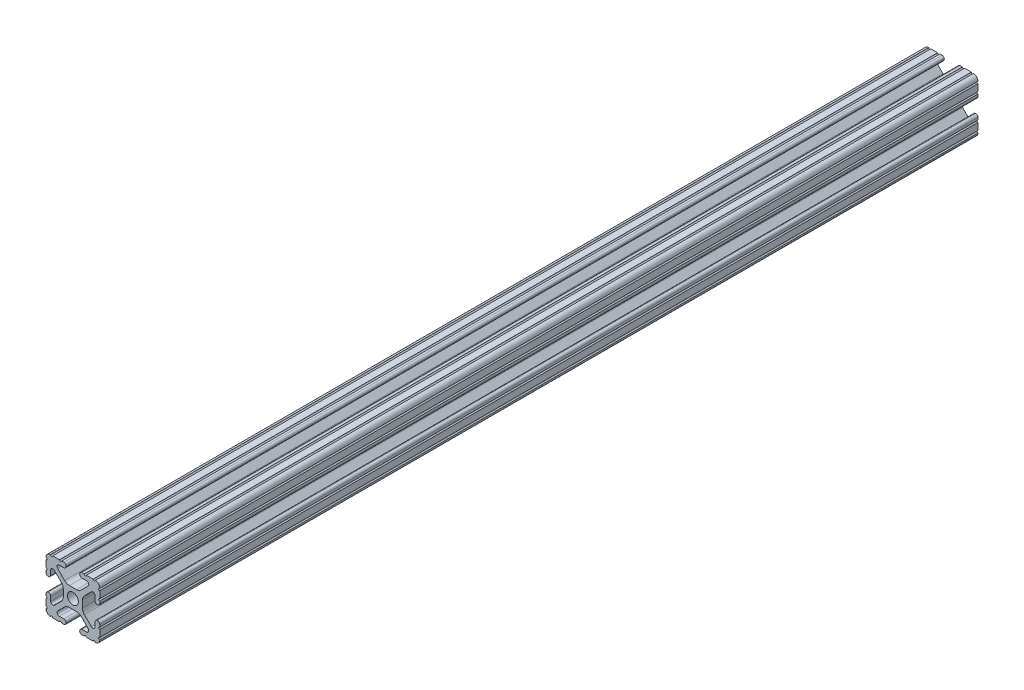
SolidWorks part; units mm, degrees
ref_plane "Front Plane" through (0, 0, 0) normal (0, 0, 1) x (1, 0, 0)
ref_plane "Top Plane" through (0, 0, 0) normal (0, 1, 0) x (1, 0, 0)
ref_plane "Right Plane" through (0, 0, 0) normal (1, 0, 0) x (0, 0, -1)
sketch "Sketch1" plane through (0, 0, 0) normal (0, 0, 1) x (1, 0, 0)
  line L88 (-7.1797, -8.6452) -> (-3.9523, -5.4237)
  line L89 (-1.7093, -4.4958) -> (1.7093, -4.4958)
  line L90 (3.9523, -5.4237) -> (7.1797, -8.6452)
  line L91 (6.4164, -10.4902) -> (4.2875, -10.4902)
  line L92 (3.2385, -11.5392) -> (3.2385, -11.651)
  line L93 (4.2875, -12.7) -> (5.3171, -12.7)
  line L94 (6.3331, -12.7) -> (9.5504, -12.7)
  line L95 (12.7, -9.5504) -> (12.7, -6.3331)
  line L96 (12.7, -5.3171) -> (12.7, -4.2875)
  line L97 (11.651, -3.2385) -> (11.5392, -3.2385)
  line L98 (10.4902, -4.2875) -> (10.4902, -6.4021)
  line L99 (8.7371, -7.1294) -> (5.441, -3.8408)
  line L100 (4.5085, -1.5932) -> (4.5085, 1.5932)
  line L101 (5.441, 3.8408) -> (8.7371, 7.1294)
  line L102 (10.4902, 6.4021) -> (10.4902, 4.2875)
  line L103 (11.5392, 3.2385) -> (11.651, 3.2385)
  line L104 (12.7, 4.2875) -> (12.7, 5.3171)
  line L105 (12.7, 6.3331) -> (12.7, 9.5504)
  line L106 (9.5504, 12.7) -> (6.3331, 12.7)
  line L107 (5.3171, 12.7) -> (4.2875, 12.7)
  line L108 (3.2385, 11.651) -> (3.2385, 11.5392)
  line L109 (4.2875, 10.4902) -> (6.4768, 10.4902)
  line L110 (7.207, 8.7244) -> (3.8983, 5.4232)
  line L111 (1.6558, 4.4958) -> (-1.6558, 4.4958)
  line L112 (-3.8983, 5.4232) -> (-7.207, 8.7244)
  line L113 (-6.4768, 10.4902) -> (-4.2875, 10.4902)
  line L114 (-3.2385, 11.5392) -> (-3.2385, 11.651)
  line L115 (-4.2875, 12.7) -> (-5.3171, 12.7)
  line L116 (-6.3331, 12.7) -> (-9.5504, 12.7)
  line L117 (-12.7, 9.5504) -> (-12.7, 6.3331)
  line L118 (-12.7, 5.3171) -> (-12.7, 4.2875)
  line L119 (-11.651, 3.2385) -> (-11.5392, 3.2385)
  line L120 (-10.4902, 4.2875) -> (-10.4902, 6.4021)
  line L121 (-8.7371, 7.1294) -> (-5.441, 3.8408)
  line L122 (-4.5085, 1.5932) -> (-4.5085, -1.5932)
  line L123 (-5.441, -3.8408) -> (-8.7371, -7.1294)
  line L124 (-10.4902, -6.4021) -> (-10.4902, -4.2875)
  line L125 (-11.5392, -3.2385) -> (-11.651, -3.2385)
  line L126 (-12.7, -4.2875) -> (-12.7, -5.3171)
  line L127 (-12.7, -6.3331) -> (-12.7, -9.5504)
  line L128 (-9.5504, -12.7) -> (-6.3331, -12.7)
  line L129 (-5.3171, -12.7) -> (-4.2875, -12.7)
  line L130 (-3.2385, -11.651) -> (-3.2385, -11.5392)
  line L131 (-4.2875, -10.4902) -> (-6.4164, -10.4902)
  circle A1 centre (0, 0) radius 2.6035
  arc A104 (-7.1797, -8.6452) -> (-6.4164, -10.4902) centre (-6.4164, -9.4098) ccw
  arc A105 (-1.7093, -4.4958) -> (-3.9523, -5.4237) centre (-1.7093, -7.6708) ccw
  arc A106 (3.9523, -5.4237) -> (1.7093, -4.4958) centre (1.7093, -7.6708) ccw
  arc A107 (6.4164, -10.4902) -> (7.1797, -8.6452) centre (6.4164, -9.4098) ccw
  arc A108 (4.2875, -10.4902) -> (3.2385, -11.5392) centre (4.2875, -11.5392) ccw
  arc A109 (3.2385, -11.651) -> (4.2875, -12.7) centre (4.2875, -11.651) ccw
  arc A110 (6.3331, -12.7) -> (5.3171, -12.7) centre (5.8251, -12.7) ccw
  arc A111 (10.5664, -12.6998) -> (9.5504, -12.7) centre (10.0584, -12.7) ccw
  arc A112 (10.5664, -12.6998) -> (12.6998, -10.5664) centre (10.5918, -10.5918) ccw
  arc A113 (12.7, -9.5504) -> (12.6998, -10.5664) centre (12.7, -10.0584) ccw
  arc A114 (12.7, -5.3171) -> (12.7, -6.3331) centre (12.7, -5.8251) ccw
  arc A115 (12.7, -4.2875) -> (11.651, -3.2385) centre (11.651, -4.2875) ccw
  arc A116 (11.5392, -3.2385) -> (10.4902, -4.2875) centre (11.5392, -4.2875) ccw
  arc A117 (8.7371, -7.1294) -> (10.4902, -6.4021) centre (9.4628, -6.4021) ccw
  arc A118 (4.5085, -1.5932) -> (5.441, -3.8408) centre (7.6835, -1.5932) ccw
  arc A119 (5.441, 3.8408) -> (4.5085, 1.5932) centre (7.6835, 1.5932) ccw
  arc A120 (10.4902, 6.4021) -> (8.7371, 7.1294) centre (9.4628, 6.4021) ccw
  arc A121 (10.4902, 4.2875) -> (11.5392, 3.2385) centre (11.5392, 4.2875) ccw
  arc A122 (11.651, 3.2385) -> (12.7, 4.2875) centre (11.651, 4.2875) ccw
  arc A123 (12.7, 6.3331) -> (12.7, 5.3171) centre (12.7, 5.8251) ccw
  arc A124 (12.6998, 10.5664) -> (12.7, 9.5504) centre (12.7, 10.0584) ccw
  arc A125 (12.6998, 10.5664) -> (10.5664, 12.6998) centre (10.5918, 10.5918) ccw
  arc A126 (9.5504, 12.7) -> (10.5664, 12.6998) centre (10.0584, 12.7) ccw
  arc A127 (5.3171, 12.7) -> (6.3331, 12.7) centre (5.8251, 12.7) ccw
  arc A128 (4.2875, 12.7) -> (3.2385, 11.651) centre (4.2875, 11.651) ccw
  arc A129 (3.2385, 11.5392) -> (4.2875, 10.4902) centre (4.2875, 11.5392) ccw
  arc A130 (7.207, 8.7244) -> (6.4768, 10.4902) centre (6.4768, 9.4563) ccw
  arc A131 (1.6558, 4.4958) -> (3.8983, 5.4232) centre (1.6558, 7.6708) ccw
  arc A132 (-3.8983, 5.4232) -> (-1.6558, 4.4958) centre (-1.6558, 7.6708) ccw
  arc A133 (-6.4768, 10.4902) -> (-7.207, 8.7244) centre (-6.4768, 9.4563) ccw
  arc A134 (-4.2875, 10.4902) -> (-3.2385, 11.5392) centre (-4.2875, 11.5392) ccw
  arc A135 (-3.2385, 11.651) -> (-4.2875, 12.7) centre (-4.2875, 11.651) ccw
  arc A136 (-6.3331, 12.7) -> (-5.3171, 12.7) centre (-5.8251, 12.7) ccw
  arc A137 (-10.5664, 12.6998) -> (-9.5504, 12.7) centre (-10.0584, 12.7) ccw
  arc A138 (-10.5664, 12.6998) -> (-12.6998, 10.5664) centre (-10.5918, 10.5918) ccw
  arc A139 (-12.7, 9.5504) -> (-12.6998, 10.5664) centre (-12.7, 10.0584) ccw
  arc A140 (-12.7, 5.3171) -> (-12.7, 6.3331) centre (-12.7, 5.8251) ccw
  arc A141 (-12.7, 4.2875) -> (-11.651, 3.2385) centre (-11.651, 4.2875) ccw
  arc A142 (-11.5392, 3.2385) -> (-10.4902, 4.2875) centre (-11.5392, 4.2875) ccw
  arc A143 (-8.7371, 7.1294) -> (-10.4902, 6.4021) centre (-9.4628, 6.4021) ccw
  arc A144 (-4.5085, 1.5932) -> (-5.441, 3.8408) centre (-7.6835, 1.5932) ccw
  arc A145 (-5.441, -3.8408) -> (-4.5085, -1.5932) centre (-7.6835, -1.5932) ccw
  arc A146 (-10.4902, -6.4021) -> (-8.7371, -7.1294) centre (-9.4628, -6.4021) ccw
  arc A147 (-10.4902, -4.2875) -> (-11.5392, -3.2385) centre (-11.5392, -4.2875) ccw
  arc A148 (-11.651, -3.2385) -> (-12.7, -4.2875) centre (-11.651, -4.2875) ccw
  arc A149 (-12.7, -6.3331) -> (-12.7, -5.3171) centre (-12.7, -5.8251) ccw
  arc A150 (-12.6998, -10.5664) -> (-12.7, -9.5504) centre (-12.7, -10.0584) ccw
  arc A151 (-12.6998, -10.5664) -> (-10.5664, -12.6998) centre (-10.5918, -10.5918) ccw
  arc A152 (-9.5504, -12.7) -> (-10.5664, -12.6998) centre (-10.0584, -12.7) ccw
  arc A153 (-5.3171, -12.7) -> (-6.3331, -12.7) centre (-5.8251, -12.7) ccw
  arc A154 (-4.2875, -12.7) -> (-3.2385, -11.651) centre (-4.2875, -11.651) ccw
  arc A155 (-3.2385, -11.5392) -> (-4.2875, -10.4902) centre (-4.2875, -11.5392) ccw
extrude "Boss-Extrude1" add sketch "Sketch1" along normal mid plane 415
